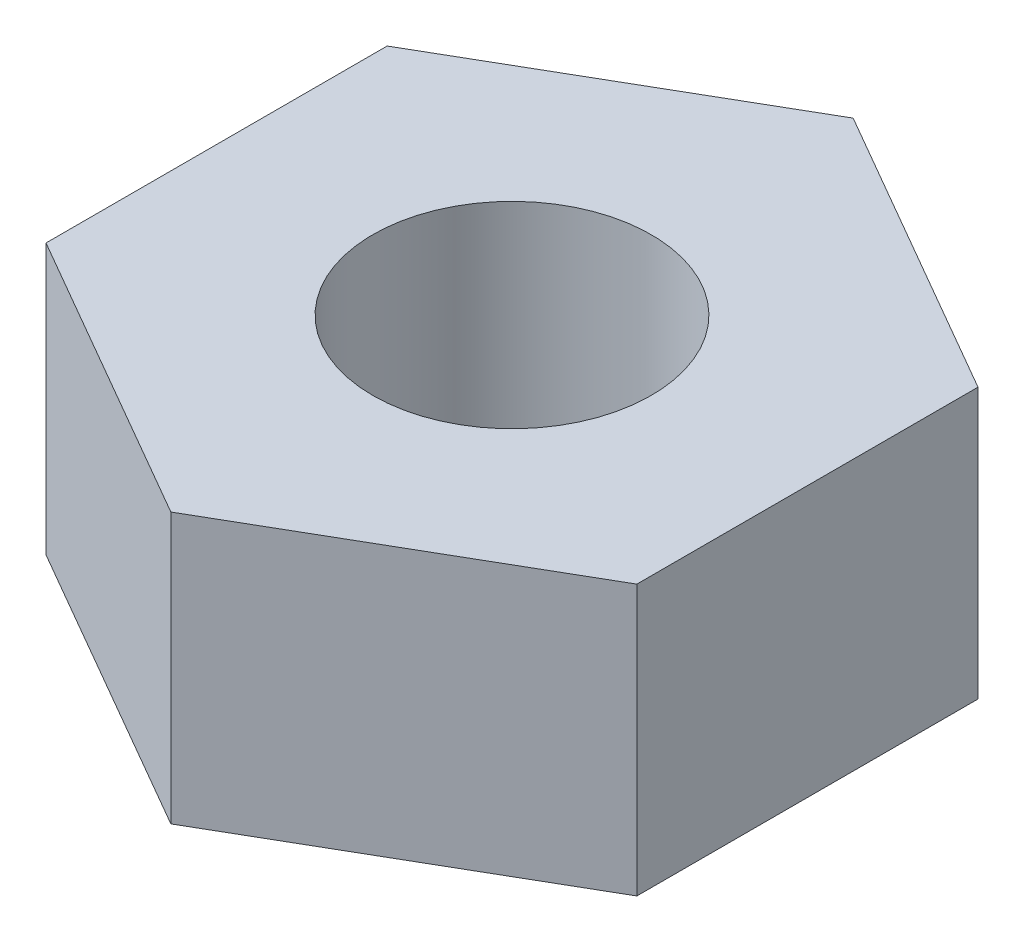
SolidWorks part; units mm, degrees
ref_plane "Спереди" through (0, 0, 0) normal (0, 0, 1) x (1, 0, 0)
ref_plane "Сверху" through (0, 0, 0) normal (0, 1, 0) x (1, 0, 0)
ref_plane "Справа" through (0, 0, 0) normal (1, 0, 0) x (0, 0, -1)
sketch "Эскиз1" plane through (0, 0, 0) normal (0, 1, 0) x (1, 0, 0)
  line L1 (0, 4.0415) -> (-3.5, 2.0207)
  line L2 (-3.5, 2.0207) -> (-3.5, -2.0207)
  line L3 (-3.5, -2.0207) -> (0, -4.0415)
  line L4 (0, -4.0415) -> (3.5, -2.0207)
  line L5 (3.5, -2.0207) -> (3.5, 2.0207)
  line L6 (3.5, 2.0207) -> (0, 4.0415)
  circle A0 centre (0, 0) radius 3.5 construction
  dimension "D1" = 7
extrude "Бобышка-Вытянуть1" add sketch "Эскиз1" along normal blind 3.2
hole_wizard "Отверстие обработанное метчиком M4x0.71" positions "Эскиз3" profile "Эскиз4" tap size "M4x0.7" standard "Ansi Metric"
sketch "Эскиз3" plane through (0, 3.2, 0) normal (0, 1, 0) x (1, 0, 0)
  point P0 (0, 0)
sketch "Эскиз4" plane through (0, 3.2, 0) normal (1, 0, 0) x (0, 0, 1)
  line L0 (0, 0) -> (0, 12.4914)
  line L1 (0, 12.4914) -> (1.65, 11.5)
  line L2 (1.65, 11.5) -> (1.65, 0)
  line L5 (1.65, 0) -> (0, 0)
  line L10 (0, 12.4914) -> (-1.65, 11.5) construction
  line L11 (0, -6.35) -> (0, 107.95) construction
  dimension "Диаметр сверла" = 3.3
  dimension "Глубина сверла" = 11.5
  dimension "Угол заточки сверла" = 118
cosmetic thread "Отверстие резьбы1" parameters "D1"=3.2, "D2"=4
